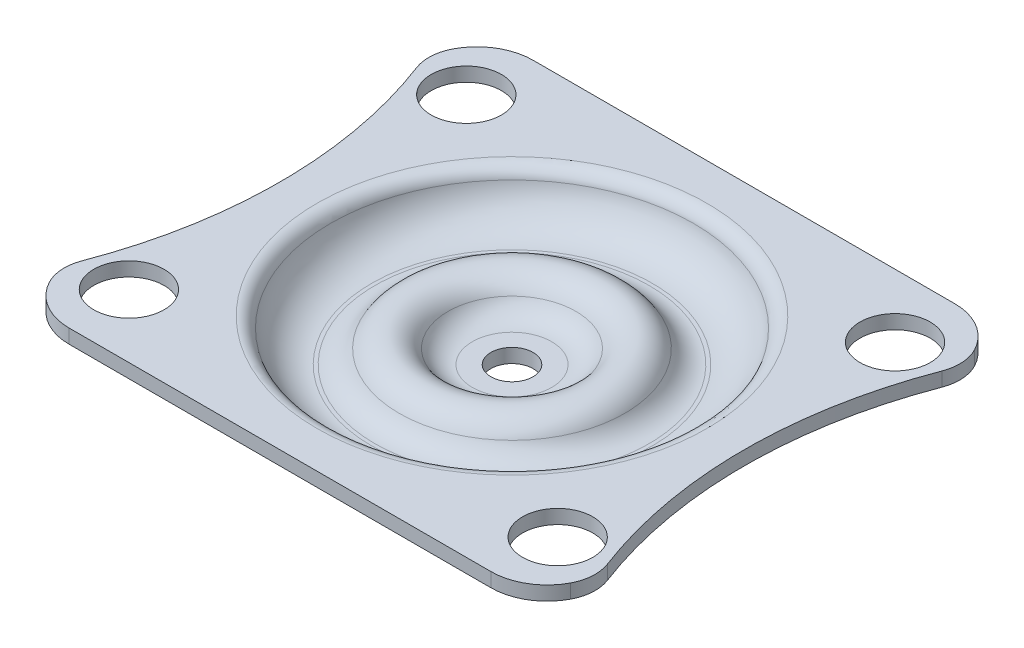
SolidWorks part; units mm, degrees
material "AISI 316 Tôle d'acier inoxydable (SS)"
ref_plane "Plan de face" through (0, 0, 0) normal (0, 0, 1) x (1, 0, 0)
ref_plane "Plan de dessus" through (0, 0, 0) normal (0, 1, 0) x (1, 0, 0)
ref_plane "Plan de droite" through (0, 0, 0) normal (1, 0, 0) x (0, 0, -1)
sketch "Esquisse1" plane through (0, 0, 0) normal (0, 0, 1) x (1, 0, 0)
  line L0 (0, 5.3737) -> (0, -9.2525) construction
  line L1 (-32.9841, 0) -> (18.5715, 0) construction
  line L2 (-32.9841, -3) -> (18.5715, -3) construction
  line L3 (-15, 0) -> (-13.873, 0)
  line L4 (-10, -3) -> (-9.75, -3)
  line L5 (-2.8218, -3) -> (-1.5, -3)
  arc A0 (-12.9047, -0.75) -> (-10, -3) centre (-10, 0) ccw
  arc A1 (-4.5538, -2) -> (-8.0179, -2) centre (-6.2859, -3) ccw
  arc A2 (-13.873, 0) -> (-12.9047, -0.75) centre (-13.873, -1) cw
  arc A3 (-9.75, -3) -> (-8.0179, -2) centre (-9.75, -1) ccw
  arc A4 (-4.5538, -2) -> (-2.8218, -3) centre (-2.8218, -1) ccw
  point P18 (-13, 0)
  point P19 (-8.2859, -3)
  point P23 (-4.2859, -3)
  dimension "D4" = 1
  dimension "D5" = 4
  dimension "D6" = 2
  dimension "D7" = 2
  dimension "D1" = 3
  dimension "D2" = 13
  dimension "D3" = 15
  dimension "D8" = 0.25
  dimension "D9" = 1.5
revolve "Révol.-Mince1" add sketch "Esquisse1" angle 360 about L0
sketch "Esquisse2" plane through (0, 0, 0) normal (0, 1, 0) x (1, 0, 0)
  line L0 (-49.1973, 0) -> (54.8272, 0) construction
  line L1 (0, 22.0018) -> (0, -20.2016) construction
  line L2 (-15, 16.5) -> (15, 16.5)
  line L3 (-15, -16.5) -> (15, -16.5)
  circle A0 centre (0, 0) radius 15
  arc A1 (-18.6865, -11.9045) -> (-18.6865, 11.9045) centre (-50, 0) ccw
  arc A2 (-15, 16.5) -> (-18.5294, 14.3824) centre (-15, 12.5) ccw
  arc A3 (-18.6865, 11.9045) -> (-18.5294, 14.3824) centre (-15.8824, 12.9706) cw
  arc A4 (-18.6865, -11.9045) -> (-18.5294, -14.3824) centre (-15.8824, -12.9706) ccw
  arc A5 (-15, -16.5) -> (-18.5294, -14.3824) centre (-15, -12.5) cw
  arc A6 (18.6865, -11.9045) -> (18.5294, -14.3824) centre (15.8824, -12.9706) cw
  arc A7 (15, -16.5) -> (18.5294, -14.3824) centre (15, -12.5) ccw
  arc A8 (18.6865, -11.9045) -> (18.6865, 11.9045) centre (50, 0) cw
  arc A9 (18.6865, 11.9045) -> (18.5294, 14.3824) centre (15.8824, 12.9706) ccw
  arc A10 (15, 16.5) -> (18.5294, 14.3824) centre (15, 12.5) cw
  circle A11 centre (-15.25, 12) radius 2.5
  circle A12 centre (-15.25, -12) radius 2.5
  circle A13 centre (15.25, 12) radius 2.5
  circle A14 centre (15.25, -12) radius 2.5
  point P13 (-16.5, 0)
  point P27 (0, -16.5)
  point P37 (0, 16.5)
  dimension "D3" = 30
  dimension "D6" = 4
  dimension "D2" = 3
  dimension "D8" = 5
  dimension "D1" = 15.25
  dimension "D4" = 16.5
  dimension "D5" = 50
  dimension "D7" = 12
extrude "Boss.-Extru.1" add sketch "Esquisse2" against normal blind 1
